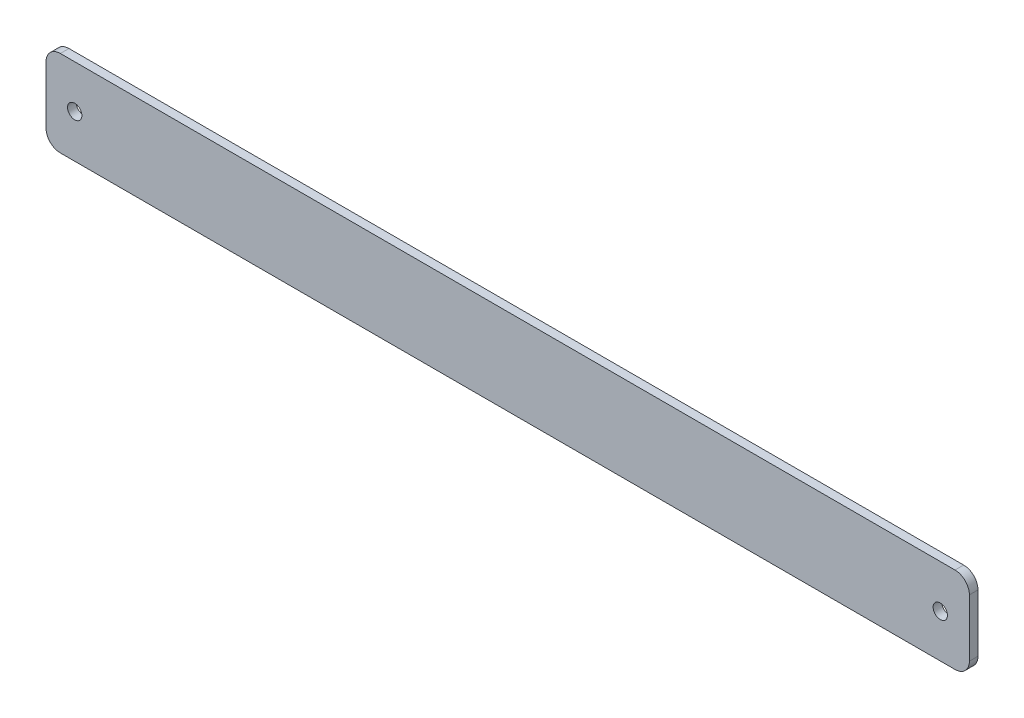
SolidWorks part; units mm, degrees
material "ply"
ref_plane "Front Plane" through (0, 0, 0) normal (0, 0, 1) x (1, 0, 0)
ref_plane "Top Plane" through (0, 0, 0) normal (0, 1, 0) x (1, 0, 0)
ref_plane "Right Plane" through (0, 0, 0) normal (1, 0, 0) x (0, 0, -1)
sketch "Sketch1" plane through (0, 0, 0) normal (0, 0, 1) x (1, 0, 0)
  line L0 (-155.75, 15) -> (155.75, 15)
  line L1 (-160.75, 10) -> (-160.75, -10)
  line L2 (-155.75, -15) -> (155.75, -15)
  line L3 (160.75, 10) -> (160.75, -10)
  line L4 (0, -15) -> (0, 15)
  line L5 (-160.75, 0) -> (160.75, 0)
  arc A0 (155.75, -15) -> (160.75, -10) centre (155.75, -10) ccw
  arc A1 (155.75, 15) -> (160.75, 10) centre (155.75, 10) cw
  arc A2 (-160.75, -10) -> (-155.75, -15) centre (-155.75, -10) ccw
  arc A3 (-155.75, 15) -> (-160.75, 10) centre (-155.75, 10) ccw
  point P8 (0, 0)
  point P12 (160.75, -15)
  point P17 (-160.75, -15)
  point P20 (-160.75, 15)
  point P27 (-160.75, -15)
  point P30 (-160.75, 15)
  dimension "D3" = 5
  dimension "D1" = 30
  dimension "D2" = 321.5
extrude "Boss-Extrude1" add sketch "Sketch1" along normal blind 3 contours A1 L0 L4 L5 L3 | L0 A3 L1 L5 L4 | L1 A2 L2 L4 L5 | L2 A0 L3 L5 L4
sketch "Sketch2" plane through (0, 0, 0) normal (0, 0, -1) x (-1, 0, 0)
  line L0 (-155.75, 15) -> (-140.75, 15)
  line L1 (-160.75, 10) -> (-160.75, -10)
  line L2 (-155.75, -15) -> (-140.75, -15)
  line L3 (-140.75, 15) -> (-140.75, -15)
  line L4 (-160.75, 10) -> (-160.75, -10) construction
  line L5 (155.75, 15) -> (-155.75, 15) construction
  line L6 (-160.75, 0) -> (-140.4911, 0)
  line L13 (0, 15) -> (0, -15)
  line L14 (155.75, -15) -> (-155.75, -15) construction
  line L15 (160.75, 10) -> (160.75, -10)
  line L16 (155.75, -15) -> (140.75, -15)
  line L17 (140.75, 15) -> (140.75, -15)
  line L18 (155.75, 15) -> (140.75, 15)
  line L19 (140.75, 0) -> (160.75, 0)
  arc A0 (-160.75, -10) -> (-155.75, -15) centre (-155.75, -10) ccw
  arc A1 (-160.75, 10) -> (-155.75, 15) centre (-155.75, 10) cw
  circle A2 centre (-150.6205, 0) radius 2.5
  arc A5 (160.75, 10) -> (155.75, 15) centre (155.75, 10) ccw
  arc A6 (160.75, -10) -> (155.75, -15) centre (155.75, -10) cw
  circle A7 centre (150.75, 0) radius 2.5
  dimension "D5" = 5
  dimension "D6" = 5
  dimension "D1" = 20
  dimension "D2" = 15
  dimension "D3" = 30
  dimension "D4" = 20
extrude "Cut-Extrude1" cut sketch "Sketch2" against normal through all contours L6 A2 | L6 A2 | A7
